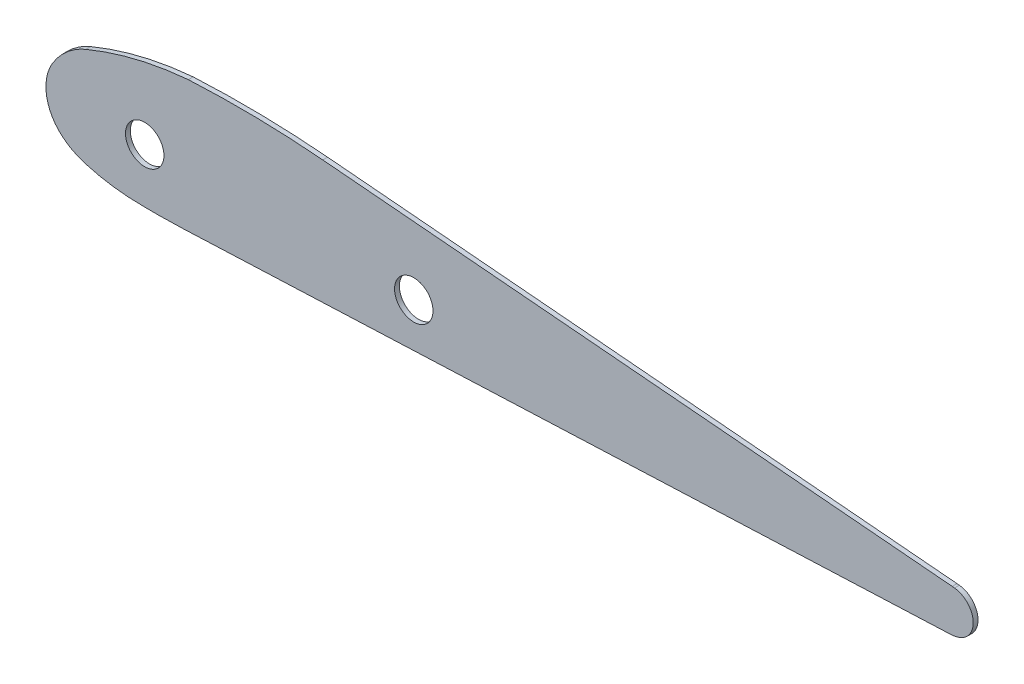
SolidWorks part; units mm, degrees
ref_plane "Front Plane" through (0, 0, 0) normal (0, 0, 1) x (1, 0, 0)
ref_plane "Top Plane" through (0, 0, 0) normal (0, 1, 0) x (1, 0, 0)
ref_plane "Right Plane" through (0, 0, 0) normal (1, 0, 0) x (0, 0, -1)
sketch "Sketch1" plane through (0, 0, 0) normal (0, 0, 1) x (1, 0, 0)
  line L0 (-1336.8893, 50.025) -> (-1752.809, 13.9378)
  line L1 (-1751.4123, -14.061) -> (-1244.4347, -35.4802)
  line L2 (0, 0) -> (0, 272.6207) construction
  line L3 (1751.4123, -14.061) -> (1244.4347, -35.4802)
  line L4 (1336.8893, 50.025) -> (1752.809, 13.9378)
  line L5 (1754.3451, 13.8031) -> (1752.809, 13.9378)
  circle A0 centre (1219.2, 0) radius 12.7
  circle A1 centre (1397, 0) radius 12.7
  spline S0 degree 5 poles (-1180.2573, 35.0088) (-1193.1397, 40.3677) (-1206.5022, 44.7577) (-1220.2023, 48.1028) (-1234.1109, 50.3692) (-1248.0664, 51.5491) knots 0 0 0 0 0 0 1 1 1 1 1 1 weights 1 1 1 1 1 1
  spline S1 degree 5 poles (-1248.0664, 51.5491) (-1265.6798, 52.4748) (-1283.368, 52.7891) (-1301.3705, 52.4801) (-1319.1568, 51.5635) (-1336.8893, 50.025) knots 0 0 0 0 0 0 1 1 1 1 1 1 weights 1 1 1 1 1 1
  spline S2 degree 5 poles (-1157.9087, 15.4237) (-1160.8878, 20.5818) (-1164.7616, 25.3362) (-1169.4286, 29.4363) (-1174.6789, 32.6883) (-1180.2573, 35.0088) knots 0 0 0 0 0 0 1 1 1 1 1 1 weights 1 1 1 1 1 1
  spline S3 degree 5 poles (-1165.1571, -22.9056) (-1158.488, -17.5352) (-1153.7228, -9.7972) (-1152.0482, -0.6613) (-1153.7152, 8.163) (-1157.9087, 15.4237) knots 0 0 0 0 0 0 1 1 1 1 1 1 weights 1 1 1 1 1 1
  spline S4 degree 5 poles (-1179.3996, -30.3822) (-1176.3086, -29.4651) (-1173.2971, -28.2439) (-1170.4089, -26.7292) (-1167.6838, -24.9403) (-1165.1571, -22.9056) knots 0 0 0 0 0 0 1 1 1 1 1 1 weights 1 1 1 1 1 1
  spline S5 degree 5 poles (-1208.3507, -35.4599) (-1202.4665, -35.1127) (-1196.5914, -34.4271) (-1190.7651, -33.4038) (-1185.0224, -32.0504) (-1179.3996, -30.3822) knots 0 0 0 0 0 0 1 1 1 1 1 1 weights 1 1 1 1 1 1
  spline S6 degree 5 poles (-1244.4347, -35.4802) (-1237.2091, -35.7854) (-1229.977, -35.9353) (-1222.7656, -35.9312) (-1215.5513, -35.7726) (-1208.3507, -35.4599) knots 0 0 0 0 0 0 1 1 1 1 1 1 weights 1 1 1 1 1 1
  spline S7 degree 5 poles (-1757.0085, -13.1026) (-1755.9211, -13.4376) (-1754.8017, -13.7051) (-1753.6933, -13.8936) (-1752.5542, -14.0125) (-1751.4123, -14.061) knots 0 0 0 0 0 0 1 1 1 1 1 1 weights 1 1 1 1 1 1
  spline S8 degree 5 poles (-1754.3451, 13.8031) (-1758.164, 13.3775) (-1761.8083, 11.6378) (-1764.657, 8.6976) (-1767.9123, 1.4018) (-1766.0369, -6.3301) (-1763.7616, -9.6997) (-1760.5669, -12.0066) (-1757.0085, -13.1026) knots 0 0 0 0 0 0 0.499137 0.499137 0.499137 1 1 1 1 1 1 weights 1 1 1 1 1 1 1 1 1
  spline S9 degree 5 poles (1754.3451, 13.8031) (1758.164, 13.3775) (1761.8083, 11.6378) (1764.657, 8.6976) (1767.9123, 1.4018) (1766.0369, -6.3301) (1763.7616, -9.6997) (1760.5669, -12.0066) (1757.0085, -13.1026) knots 0 0 0 0 0 0 0.499137 0.499137 0.499137 1 1 1 1 1 1 weights 1 1 1 1 1 1 1 1 1
  spline S10 degree 5 poles (1757.0085, -13.1026) (1755.9211, -13.4376) (1754.8017, -13.7051) (1753.6933, -13.8936) (1752.5542, -14.0125) (1751.4123, -14.061) knots 0 0 0 0 0 0 1 1 1 1 1 1 weights 1 1 1 1 1 1
  spline S11 degree 5 poles (1244.4347, -35.4802) (1237.2091, -35.7854) (1229.977, -35.9353) (1222.7656, -35.9312) (1215.5513, -35.7726) (1208.3507, -35.4599) knots 0 0 0 0 0 0 1 1 1 1 1 1 weights 1 1 1 1 1 1
  spline S12 degree 5 poles (1208.3507, -35.4599) (1202.4665, -35.1127) (1196.5914, -34.4271) (1190.7651, -33.4038) (1185.0224, -32.0504) (1179.3996, -30.3822) knots 0 0 0 0 0 0 1 1 1 1 1 1 weights 1 1 1 1 1 1
  spline S13 degree 5 poles (1179.3996, -30.3822) (1176.3086, -29.4651) (1173.2971, -28.2439) (1170.4089, -26.7292) (1167.6838, -24.9403) (1165.1571, -22.9056) knots 0 0 0 0 0 0 1 1 1 1 1 1 weights 1 1 1 1 1 1
  spline S14 degree 5 poles (1165.1571, -22.9056) (1158.488, -17.5352) (1153.7228, -9.7972) (1152.0482, -0.6613) (1153.7152, 8.163) (1157.9087, 15.4237) knots 0 0 0 0 0 0 1 1 1 1 1 1 weights 1 1 1 1 1 1
  spline S15 degree 5 poles (1157.9087, 15.4237) (1160.8878, 20.5818) (1164.7616, 25.3362) (1169.4286, 29.4363) (1174.6789, 32.6883) (1180.2573, 35.0088) knots 0 0 0 0 0 0 1 1 1 1 1 1 weights 1 1 1 1 1 1
  spline S16 degree 5 poles (1248.0664, 51.5491) (1265.6798, 52.4748) (1283.368, 52.7891) (1301.3705, 52.4801) (1319.1568, 51.5635) (1336.8893, 50.025) knots 0 0 0 0 0 0 1 1 1 1 1 1 weights 1 1 1 1 1 1
  spline S17 degree 5 poles (1180.2573, 35.0088) (1193.1397, 40.3677) (1206.5022, 44.7577) (1220.2023, 48.1028) (1234.1109, 50.3692) (1248.0664, 51.5491) knots 0 0 0 0 0 0 1 1 1 1 1 1 weights 1 1 1 1 1 1
  point P12 (0, 0)
  point P32 (0, 0)
  point P33 (1284.061, -73.4153)
  point P34 (0, 0)
  dimension "D2" = 25.4
  dimension "D3" = 25.4
  dimension "D1" = 38.3293
  dimension "D4" = 1219.2
  dimension "D5" = 1397
extrude "Boss-Extrude1" add sketch "Sketch1" along normal blind 3.175 contours S17 S15 S14 S13 S12 S11 L3 S10 S9 L5 L4 S16 A1 A0
